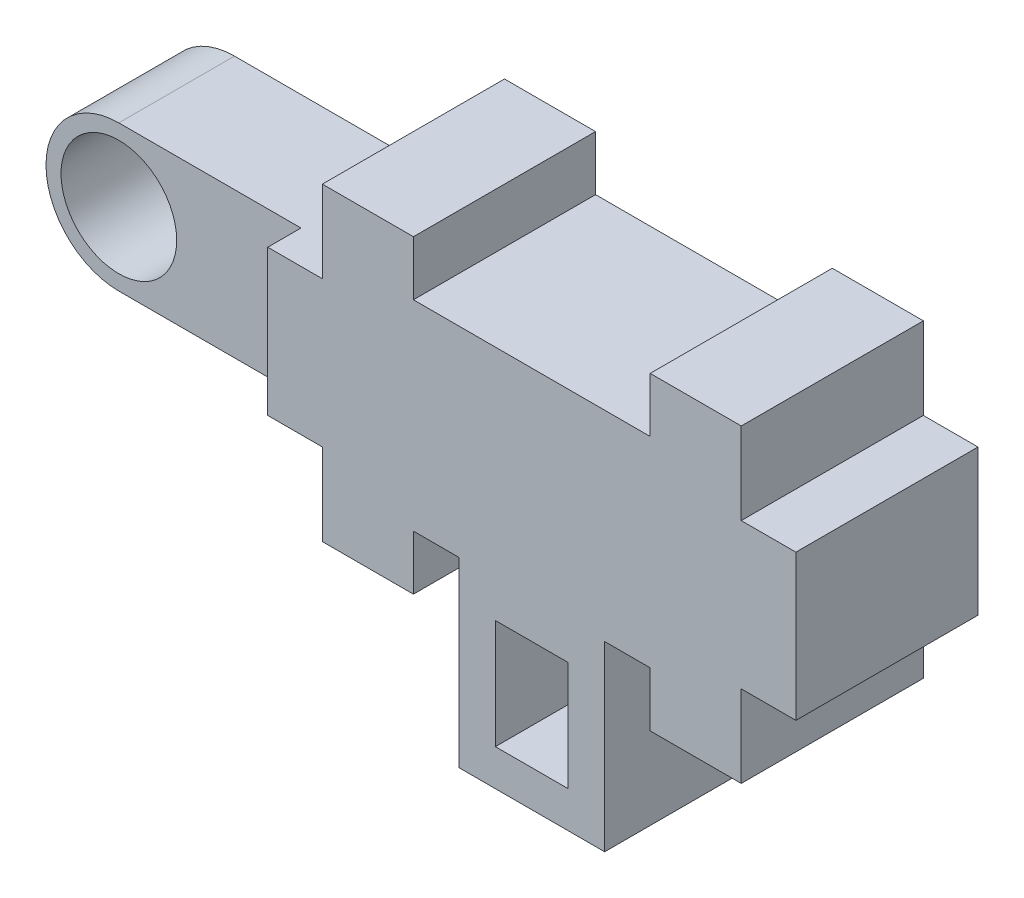
SolidWorks part; units mm, degrees
material "ABS"
ref_plane "Front Plane" through (0, 0, 0) normal (0, 0, 1) x (1, 0, 0)
ref_plane "Top Plane" through (0, 0, 0) normal (0, 1, 0) x (1, 0, 0)
ref_plane "Right Plane" through (0, 0, 0) normal (1, 0, 0) x (0, 0, -1)
sketch "Sketch1" plane through (0, 0, 0) normal (0, 0, 1) x (1, 0, 0)
  line L0 (-2.9009, 0.4669) -> (-2.9009, 6.4669) construction
  line L1 (-2.9009, 6.4669) -> (8.0991, 6.4669) construction
  line L2 (8.0991, 6.4669) -> (8.0991, 0.4669) construction
  line L3 (8.0991, 0.4669) -> (-2.9009, 0.4669) construction
  line L4 (5.5991, 6.4669) -> (5.5991, 7.9669) construction
  line L5 (5.5991, 7.9669) -> (8.5991, 7.9669) construction
  line L6 (8.5991, 7.9669) -> (8.5991, 5.7169) construction
  line L7 (8.5991, 5.7169) -> (10.0991, 5.7169) construction
  line L8 (10.0991, 5.7169) -> (10.0991, 1.2169) construction
  line L9 (10.0991, 1.2169) -> (8.5991, 1.2169) construction
  line L10 (8.5991, 1.2169) -> (8.5991, -1.0331) construction
  line L11 (8.5991, -1.0331) -> (5.5991, -1.0331) construction
  line L12 (5.5991, -1.0331) -> (5.5991, 0.4669) construction
  line L13 (5.5991, 0.4669) -> (4.8491, 0.4669) construction
  line L14 (5.5991, 6.4669) -> (-0.4009, 6.4669) construction
  line L15 (-0.4009, 7.9669) -> (-3.4009, 7.9669) construction
  line L16 (-0.4009, -1.0331) -> (-0.4009, 0.4669) construction
  line L17 (-3.4009, -1.0331) -> (-0.4009, -1.0331) construction
  line L18 (-3.4009, 1.2169) -> (-3.4009, -1.0331) construction
  line L19 (-4.9009, 1.2169) -> (-3.4009, 1.2169) construction
  line L20 (-4.9009, 5.7169) -> (-4.9009, 1.2169) construction
  line L21 (-3.4009, 5.7169) -> (-4.9009, 5.7169) construction
  line L22 (-3.4009, 7.9669) -> (-3.4009, 5.7169) construction
  line L23 (-0.4009, 6.4669) -> (-0.4009, 7.9669) construction
  line L24 (0.3491, 0.4669) -> (-0.4009, 0.4669) construction
  line L25 (4.8491, 0.4669) -> (4.8491, -1.5331) construction
  line L26 (4.8491, -1.5331) -> (0.3491, -1.5331) construction
  line L27 (0.3491, -1.5331) -> (0.3491, 0.4669) construction
  line L28 (-0.6509, 7.7169) -> (-3.1509, 7.7169)
  line L29 (-3.1509, 7.7169) -> (-3.1509, 5.4669)
  line L30 (-3.1509, 5.4669) -> (-4.6509, 5.4669)
  line L31 (-4.6509, 5.4669) -> (-4.6509, 1.4669)
  line L32 (-4.6509, 1.4669) -> (-3.1509, 1.4669)
  line L33 (-3.1509, 1.4669) -> (-3.1509, -0.7831)
  line L34 (-3.1509, -0.7831) -> (-0.6509, -0.7831)
  line L35 (-0.6509, -0.7831) -> (-0.6509, 0.7169)
  line L36 (0.5991, 0.7169) -> (-0.6509, 0.7169)
  line L37 (0.5991, 0.7169) -> (0.5991, -4.2831)
  line L39 (4.5991, 0.7169) -> (4.5991, 0.4669)
  line L40 (5.8491, 0.7169) -> (4.5991, 0.7169)
  line L41 (5.8491, -0.7831) -> (5.8491, 0.7169)
  line L42 (8.3491, -0.7831) -> (5.8491, -0.7831)
  line L43 (8.3491, 1.4669) -> (8.3491, -0.7831)
  line L44 (9.8491, 1.4669) -> (8.3491, 1.4669)
  line L45 (9.8491, 5.4669) -> (9.8491, 1.4669)
  line L46 (8.3491, 5.4669) -> (9.8491, 5.4669)
  line L47 (8.3491, 7.7169) -> (8.3491, 5.4669)
  line L48 (5.8491, 7.7169) -> (8.3491, 7.7169)
  line L49 (5.8491, 6.2169) -> (5.8491, 7.7169)
  line L50 (5.8491, 6.2169) -> (-0.6509, 6.2169)
  line L51 (-0.6509, 6.2169) -> (-0.6509, 7.7169)
  line L52 (0.5991, -4.2831) -> (4.5991, -4.2831)
  line L53 (0.5991, -1.2831) -> (0.5991, 0.7169) construction
  line L54 (4.5991, -4.2831) -> (4.5991, 0.4669)
  line L55 (4.5991, 0.7169) -> (4.5991, -1.2831) construction
  line L56 (4.5991, -1.2831) -> (0.5991, -1.2831) construction
  point P20 (2.5991, 0.4669)
  point P27 (2.5991, 6.4669)
  dimension "D1" = 0.25
extrude "Boss-Extrude1" add sketch "Sketch1" against normal blind 5
sketch "Sketch2" plane through (-4.6509, 0, 0) normal (-1, 0, 0) x (0, 0, 1)
  line L0 (-2.5, 5.4669) -> (-2.5, 1.4669) construction
  line L2 (-5, 5.4669) -> (0, 5.4669) construction
  line L3 (-5, 1.4669) -> (0, 1.4669) construction
  line L4 (-4.0875, 5.4669) -> (-0.9125, 5.4669)
  line L6 (-0.9125, 5.4669) -> (-0.9125, 1.4669)
  line L10 (-0.9125, 1.4669) -> (-4.0875, 1.4669)
  line L11 (-4.0875, 1.4669) -> (-4.0875, 5.4669)
  point P10 (-2.5, 5.4669)
  dimension "D2" = 3.175
extrude "Boss-Extrude2" add sketch "Sketch2" along normal blind 7
sketch "Sketch5" plane through (0, 0, -0.9125) normal (0, 0, 1) x (1, 0, 0)
  line L0 (-11.6509, 5.4669) -> (-4.6509, 5.4669) construction
  line L3 (-11.6509, 1.4669) -> (-4.6509, 1.4669) construction
  line L6 (-11.6509, 1.4669) -> (-11.6509, 5.4669) construction
  line L7 (-9.6509, 5.4669) -> (-11.6509, 5.4669)
  line L8 (-11.6509, 5.4669) -> (-11.6509, 3.4669)
  line L9 (-11.6509, 3.4669) -> (-11.6509, 1.4669)
  line L10 (-11.6509, 1.4669) -> (-9.6509, 1.4669)
  arc A0 (-9.6509, 5.4669) -> (-9.6509, 1.4669) centre (-9.6509, 3.4669) ccw
  circle A1 centre (-9.6509, 3.4669) radius 1.5875
  line M15 (-4.6509, 5.4669) -> (-11.6509, 5.4669)
  line M16 (-11.6509, 5.4669) -> (-11.6509, 1.4669)
  line M17 (-11.6509, 1.4669) -> (-4.6509, 1.4669)
extrude "Cut-Extrude3" cut sketch "Sketch5" against normal up to surface (3.175 mm away) contours A0 M15 M16 | A0 M16 M17 | A1 up to face at (-9.9009, 3.9669, -4.0875)
sketch "Sketch6" plane through (0, 0, 0) normal (0, 0, 1) x (1, 0, 0)
  line L0 (4.5991, -1.2831) -> (0.5991, -1.2831) construction
  line L4 (4.5991, 0.7169) -> (5.8491, 0.7169) construction
  line L5 (1.5991, -3.2831) -> (1.5991, -0.2831)
  line L6 (1.5991, -0.2831) -> (3.5991, -0.2831)
  line L7 (3.5991, -0.2831) -> (3.5991, -3.2831)
  line L8 (3.5991, -3.2831) -> (1.5991, -3.2831)
  line L9 (0.5991, -4.2831) -> (4.5991, -4.2831) construction
  line L10 (4.5991, -4.2831) -> (4.5991, 0.7169) construction
  line L11 (0.5991, 0.7169) -> (0.5991, -4.2831) construction
  point P4 (5.2241, 0.7169)
  dimension "D1" = 2
  dimension "D2" = 1
  dimension "D3" = 1
  dimension "D4" = 3
  dimension "D5" = 1
extrude "Cut-Extrude4" cut sketch "Sketch6" against normal up to surface (5 mm away) up to face at (2.5991, 2.5919, -5)
sketch "Sketch7" plane through (0, -4.2831, 0) normal (0, -1, 0) x (1, 0, 0)
  line L0 (2.5991, 0) -> (2.5991, -5) construction
  line L1 (0.5991, 0) -> (4.5991, 0) construction
  line L2 (0.5991, -5) -> (4.5991, -5) construction
  circle A0 centre (2.5991, -2.5) radius 0.75
extrude "Cut-Extrude5" cut sketch "Sketch7" against normal up to surface (1 mm away) up to face at (2.5991, -3.2831, -2.5)
